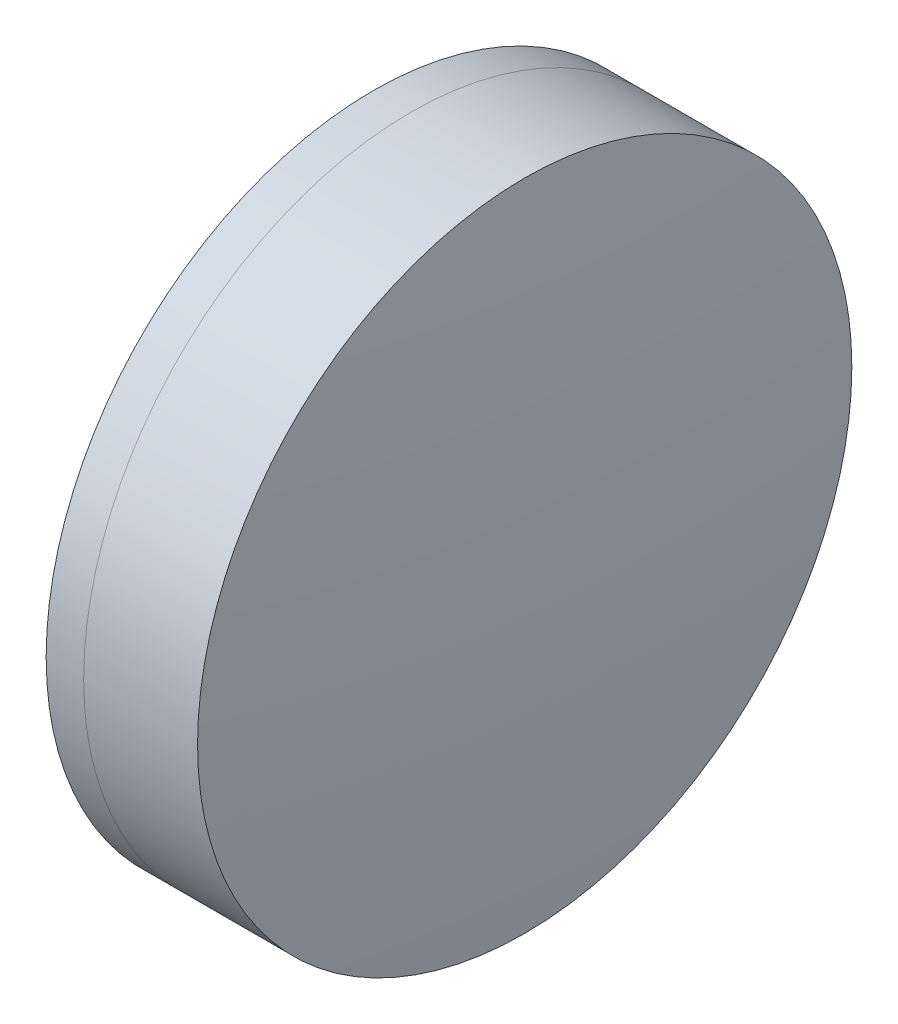
SolidWorks part; units mm, degrees
ref_plane "前视基准面" through (0, 0, 0) normal (0, 0, 1) x (1, 0, 0)
ref_plane "上视基准面" through (0, 0, 0) normal (0, 1, 0) x (1, 0, 0)
ref_plane "右视基准面" through (0, 0, 0) normal (1, 0, 0) x (0, 0, -1)
sketch "草图1" plane through (0, 0, 0) normal (0, 1, 0) x (1, 0, 0)
  line L0 (124.5233, 0) -> (646.9917, 0) construction
  line L1 (284.6157, -12.7) -> (286.0709, -12.7)
  line L2 (284.6157, 12.7) -> (286.0709, 12.7)
  arc A0 (286.0709, -12.7) -> (286.0709, 12.7) centre (264.479, 0) ccw
  arc A1 (284.6157, 12.7) -> (284.6157, -12.7) centre (311.109, 0) ccw
  point P10 (281.729, 0)
  point P11 (289.529, 0)
  dimension "D3" = 29.38
  dimension "D4" = 25.05
  dimension "D1" = 12.7
  dimension "D2" = 12.7
  dimension "D5" = 7.8
revolve "旋转1" add sketch "草图1" angle 360 about L0
sketch "草图2" plane through (0, 0, 0) normal (0, 1, 0) x (1, 0, 0)
  line L0 (-0.5519, 0) -> (622.6607, 0) construction
  line L2 (286.0709, 12.7) -> (290.4927, 12.7)
  line L3 (286.0709, -12.7) -> (290.4927, -12.7)
  arc A0 (290.4927, -12.7) -> (290.4927, 12.7) centre (164.069, 0) ccw
  arc A1 (286.0709, -12.7) -> (286.0709, 12.7) centre (264.479, 0) ccw construction
  arc A2 (286.0709, -12.7) -> (286.0709, 12.7) centre (264.479, 0) ccw
  point P4 (289.529, 0)
  point P8 (291.129, 0)
  dimension "D1" = 127.06
  dimension "D2" = 1.6
revolve "旋转3" add sketch "草图2" angle 360 about L0
